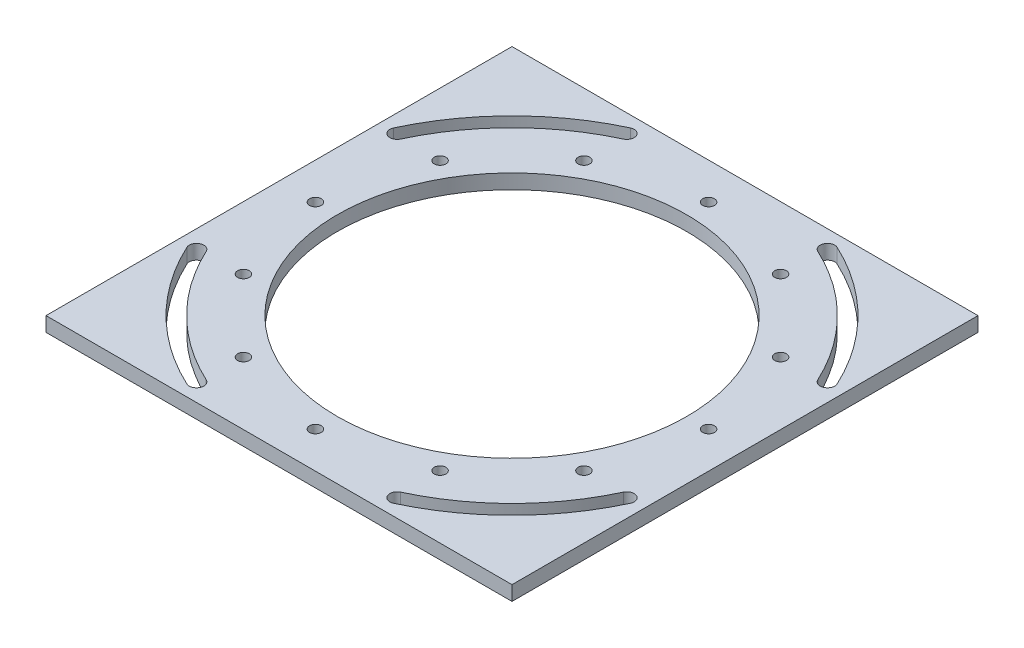
SolidWorks part; units mm, degrees
ref_plane "Front Plane" through (0, 0, 0) normal (0, 0, 1) x (1, 0, 0)
ref_plane "Top Plane" through (0, 0, 0) normal (0, 1, 0) x (1, 0, 0)
ref_plane "Right Plane" through (0, 0, 0) normal (1, 0, 0) x (0, 0, -1)
sketch "Sketch1" plane through (0, 0, 0) normal (0, 1, 0) x (1, 0, 0)
  line L1 (-101.6, 101.6) -> (101.6, 101.6)
  line L2 (-101.6, 101.6) -> (-101.6, -101.6)
  line L3 (-101.6, -101.6) -> (101.6, -101.6)
  line L4 (101.6, 101.6) -> (101.6, -101.6)
  line L5 (-101.6, 101.6) -> (101.6, -101.6) construction
  line L6 (-101.6, -101.6) -> (101.6, 101.6) construction
  point P0 (0, 0)
  dimension "D1" = 203.2
  dimension "D2" = 203.2
extrude "Boss-Extrude1" add sketch "Sketch1" along normal blind 6.35
sketch "Sketch2" plane through (0, 6.35, 0) normal (0, 1, 0) x (1, 0, 0)
  circle A0 centre (0, 0) radius 76.2
  dimension "D1" = 152.4
extrude "Cut-Extrude1" cut sketch "Sketch2" against normal up to next
hole_wizard "1/4-20 Tapped Hole1" positions "Sketch4" profile "Sketch3" tap size "1/4-20" standard "ANSI Inch" end condition up to next
sketch "Sketch4" plane through (0, 6.35, 0) normal (0, 1, 0) x (1, 0, 0)
  line L0 (0, 0) -> (0, 85.725)
  circle A0 centre (0, 0) radius 85.725
  point P7 (0, 85.725)
  dimension "D1" = 171.45
sketch "Sketch3" plane through (0, 6.35, -85.725) normal (1, 0, 0) x (0, 0, 1)
  line L0 (0, 0) -> (0, 6.351)
  line L1 (0, 6.351) -> (2.5527, 6.351)
  line L2 (2.5527, 6.351) -> (2.5527, 0)
  line L5 (2.5527, 0) -> (0, 0)
  line L11 (0, -6.35) -> (0, 107.95) construction
  dimension "Thread Major Dia." = 5.1054
  dimension "Thru Tap Drill Depth" = 6.351
pattern_circular "CirPattern1" count 12 every 30 about axis through (0, 0, 0) along (0, 1, 0) of "1/4-20 Tapped Hole1"
sketch "Sketch5" plane through (0, 6.35, 0) normal (0, 1, 0) x (1, 0, 0)
  line L0 (73.1891, 73.1891) -> (-73.1891, -73.1891) construction
  line L1 (-73.1891, 73.1891) -> (73.1891, -73.1891) construction
  line L2 (0, 0) -> (43.7431, 93.8074) construction
  line L3 (0, 0) -> (93.8074, 43.7431) construction
  line L4 (0, 0) -> (0, 85.725) construction
  arc A0 (-93.8074, 43.7431) -> (-43.7431, 93.8074) centre (0, 0) cw construction
  arc A1 (-45.0849, 96.6849) -> (-96.6849, 45.0849) centre (0, 0) ccw
  arc A2 (-42.4013, 90.9299) -> (-90.9299, 42.4013) centre (0, 0) ccw
  arc A3 (-42.4013, 90.9299) -> (-45.0849, 96.6849) centre (-43.7431, 93.8074) ccw
  arc A4 (-96.6849, 45.0849) -> (-90.9299, 42.4013) centre (-93.8074, 43.7431) ccw
  circle A5 centre (0, 0) radius 103.505 construction
  arc A6 (93.8074, 43.7431) -> (43.7431, 93.8074) centre (0, 0) ccw construction
  arc A7 (96.6849, 45.0849) -> (45.0849, 96.6849) centre (0, 0) ccw
  arc A8 (90.9299, 42.4013) -> (42.4013, 90.9299) centre (0, 0) ccw
  arc A9 (90.9299, 42.4013) -> (96.6849, 45.0849) centre (93.8074, 43.7431) ccw
  arc A10 (45.0849, 96.6849) -> (42.4013, 90.9299) centre (43.7431, 93.8074) ccw
  arc A11 (-43.7431, -93.8074) -> (-93.8074, -43.7431) centre (0, 0) cw construction
  arc A12 (-96.6849, -45.0849) -> (-45.0849, -96.6849) centre (0, 0) ccw
  arc A13 (-90.9299, -42.4013) -> (-42.4013, -90.9299) centre (0, 0) ccw
  arc A14 (-90.9299, -42.4013) -> (-96.6849, -45.0849) centre (-93.8074, -43.7431) ccw
  arc A15 (-45.0849, -96.6849) -> (-42.4013, -90.9299) centre (-43.7431, -93.8074) ccw
  arc A16 (93.8074, -43.7431) -> (43.7431, -93.8074) centre (0, 0) cw construction
  arc A17 (45.0849, -96.6849) -> (96.6849, -45.0849) centre (0, 0) ccw
  arc A18 (42.4013, -90.9299) -> (90.9299, -42.4013) centre (0, 0) ccw
  arc A19 (42.4013, -90.9299) -> (45.0849, -96.6849) centre (43.7431, -93.8074) ccw
  arc A20 (96.6849, -45.0849) -> (90.9299, -42.4013) centre (93.8074, -43.7431) ccw
  point P4 (-73.1891, 73.1891)
  point P13 (73.1891, 73.1891)
  point P22 (-73.1891, -73.1891)
  point P27 (73.1891, -73.1891)
  dimension "D1" = 207.01
  dimension "D4" = 3.175
  dimension "D2" = 45
  dimension "D3" = 45
  dimension "D5" = 40
extrude "Cut-Extrude2" cut sketch "Sketch5" against normal up to next
